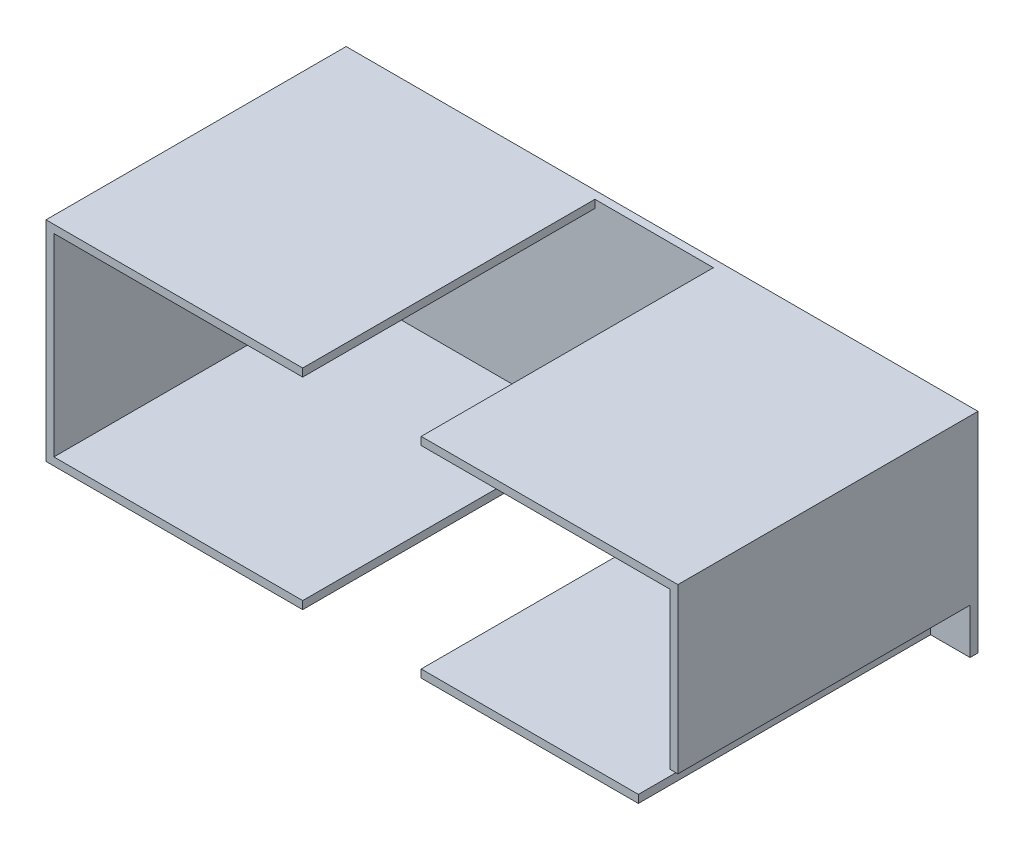
SolidWorks part; units mm, degrees
material "ABS"
ref_plane "Front Plane" through (0, 0, 0) normal (0, 0, 1) x (1, 0, 0)
ref_plane "Top Plane" through (0, 0, 0) normal (0, 1, 0) x (1, 0, 0)
ref_plane "Right Plane" through (0, 0, 0) normal (1, 0, 0) x (0, 0, -1)
sketch "Sketch1" plane through (0, 0, 0) normal (0, 0, 1) x (1, 0, 0)
  line L1 (-80, -26.5) -> (80, -26.5)
  line L2 (-80, -26.5) -> (-80, 26.5)
  line L3 (-80, 26.5) -> (80, 26.5)
  line L4 (80, -26.5) -> (80, 26.5)
  line L5 (-80, -26.5) -> (80, 26.5) construction
  line L6 (-80, 26.5) -> (80, -26.5) construction
  point P0 (0, 0)
  dimension "D1" = 53
  dimension "D2" = 160
extrude "Boss-Extrude1" add sketch "Sketch1" along normal blind 76
sketch "Sketch2" plane through (0, 0, 76) normal (0, 0, 1) x (1, 0, 0)
  line L8 (78, -24.5) -> (78, 24.5)
  line L9 (78, 24.5) -> (-78, 24.5)
  line L10 (-78, 24.5) -> (-78, -24.5)
  line L11 (-78, -24.5) -> (78, -24.5)
  line L12 (78, -24.5) -> (78, 24.5)
  line L13 (78, 24.5) -> (-78, 24.5)
  line L14 (-78, 24.5) -> (-78, -24.5)
  line L15 (-78, -24.5) -> (78, -24.5)
  dimension "D1" = 2
extrude "Cut-Extrude1" cut sketch "Sketch2" against normal offset from surface (74 mm away) 2 up to face at (0, 0, 0)
sketch "Sketch3" plane through (0, 0, 2) normal (0, 0, 1) x (1, 0, 0)
  line L0 (-101.1663, 0) -> (96.2254, 0) construction
  line L1 (-50, 13.8617) -> (-50, -14.5931) construction
  line L2 (50, 13.8617) -> (50, -14.5931) construction
  circle A0 centre (50, 0) radius 2
  circle A1 centre (-50, 0) radius 2
  dimension "D3" = 4
  dimension "D4" = 4
  dimension "D1" = 50
  dimension "D2" = 50
extrude "Cut-Extrude2" cut sketch "Sketch3" against normal up to next
sketch "Sketch4" plane through (0, 0, 76) normal (0, 0, 1) x (1, 0, 0)
  line L0 (0, 41.5568) -> (0, -44.6366) construction
  line L1 (-97.4103, 0) -> (94.3981, 0) construction
  line L2 (78, 24.5) -> (-78, 24.5) construction
  line L3 (-15, 24.5) -> (15, 24.5)
  line L4 (-15, 24.5) -> (-15, 26.5)
  line L5 (-15, 26.5) -> (15, 26.5)
  line L6 (15, 24.5) -> (15, 26.5)
  line L7 (-15, 24.5) -> (15, 26.5) construction
  line L8 (-15, 26.5) -> (15, 24.5) construction
  line L9 (-15, -26.5) -> (15, -26.5)
  line L10 (-15, -26.5) -> (-15, -24.5)
  line L11 (-15, -24.5) -> (15, -24.5)
  line L12 (15, -26.5) -> (15, -24.5)
  line L13 (-15, -26.5) -> (15, -24.5) construction
  line L14 (-15, -24.5) -> (15, -26.5) construction
  line L15 (90, -15) -> (70, -15)
  line L16 (90, -15) -> (90, -35)
  line L17 (90, -35) -> (70, -35)
  line L18 (70, -15) -> (70, -35)
  line L19 (80, 26.5) -> (-80, 26.5) construction
  line L20 (-78, -24.5) -> (78, -24.5) construction
  line L21 (-80, -26.5) -> (80, -26.5) construction
  point P5 (0, 25.5)
  point P10 (0, -25.5)
  dimension "D1" = 30
  dimension "D2" = 30
  dimension "D3" = 15
  dimension "D4" = 70
  dimension "D5" = 20
  dimension "D6" = 20
extrude "Cut-Extrude3" cut sketch "Sketch4" against normal up to surface (74 mm away) up to face at (52, 0, 2)
